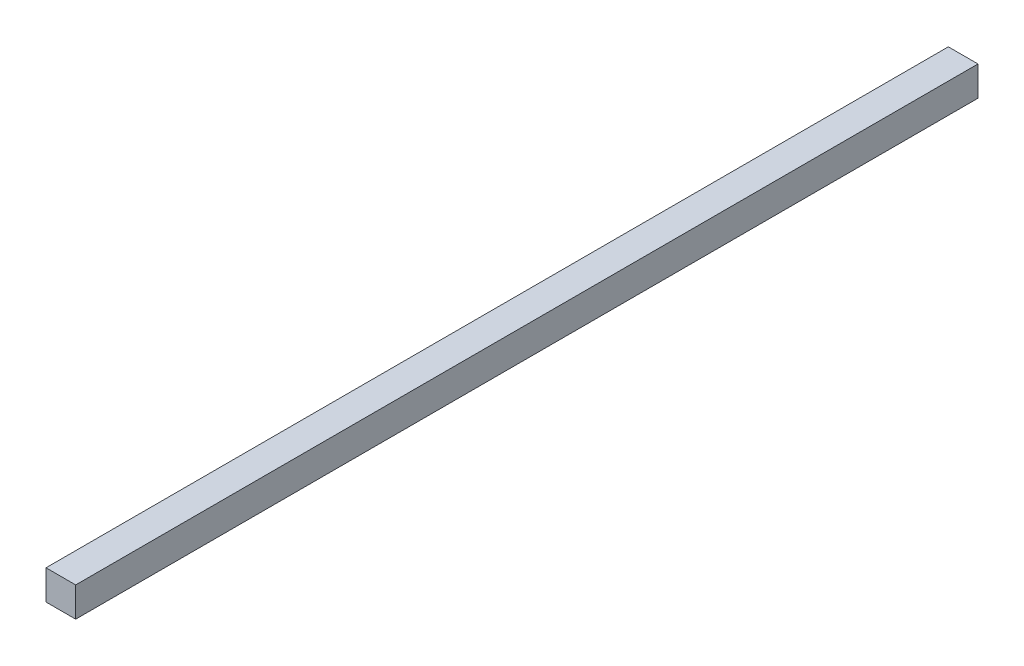
SolidWorks part; units mm, degrees
material "Plywood"
ref_plane "Front Plane" through (0, 0, 0) normal (0, 0, 1) x (1, 0, 0)
ref_plane "Top Plane" through (0, 0, 0) normal (0, 1, 0) x (1, 0, 0)
ref_plane "Right Plane" through (0, 0, 0) normal (1, 0, 0) x (0, 0, -1)
sketch "Sketch1" plane through (0, 0, 0) normal (1, 0, 0) x (0, 0, -1)
  line L0 (0, 12.7) -> (0, 0)
  line L1 (0, 0) -> (386.08, 0)
  line L3 (0, 12.7) -> (386.08, 12.7)
  line L4 (386.08, 0) -> (386.08, 12.7)
  dimension "D1" = 12.7
  dimension "D2" = 386.08
extrude "Boss-Extrude1" add sketch "Sketch1" along normal blind 12.7
